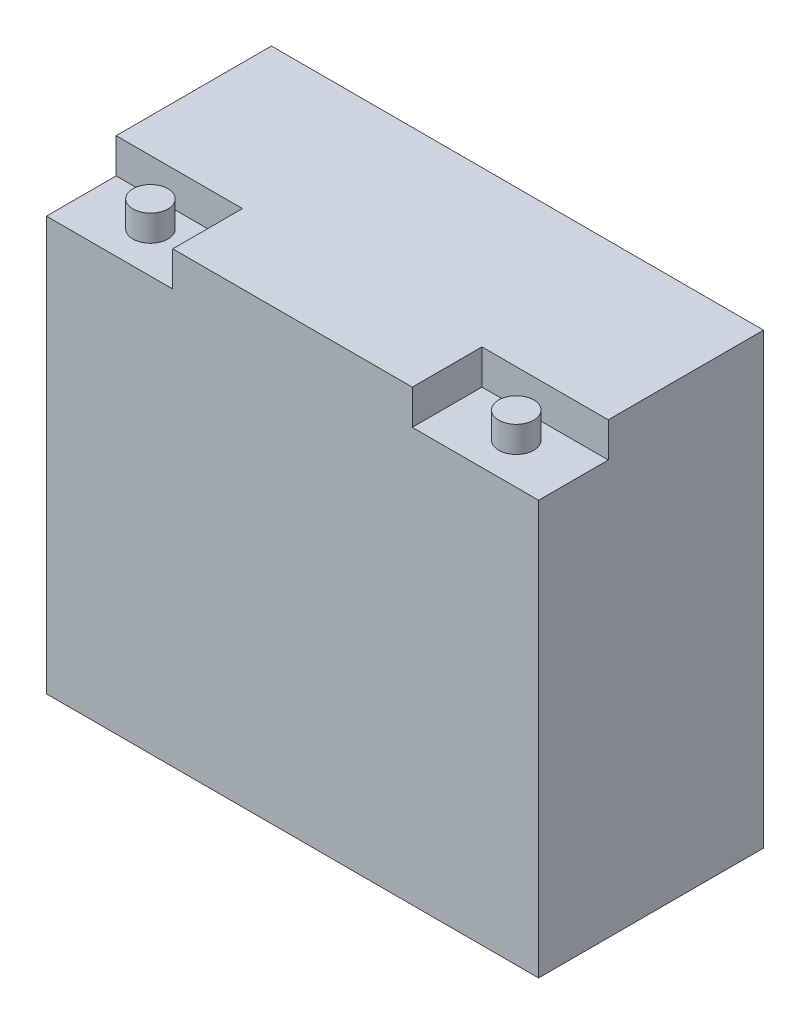
SolidWorks part; units mm, degrees
ref_plane "Front" through (0, 0, 0) normal (0, 0, 1) x (1, 0, 0)
ref_plane "Top" through (0, 0, 0) normal (0, 1, 0) x (1, 0, 0)
ref_plane "Right" through (0, 0, 0) normal (1, 0, 0) x (0, 0, -1)
sketch "Sketch1" plane through (0, 0, 0) normal (0, 1, 0) x (1, 0, 0)
  line L1 (0, 0) -> (179.3875, 0)
  line L2 (0, 0) -> (0, 82.0057)
  line L3 (0, 82.0057) -> (179.3875, 82.0057)
  line L4 (179.3875, 0) -> (179.3875, 82.0057)
  line L5 (0, 0) -> (179.3875, 82.0057) construction
  line L6 (0, 82.0057) -> (179.3875, 0) construction
  point P4 (89.6938, 41.0029)
  dimension "D1" = 179.3875
  dimension "D2" = 82.0057
extrude "Boss-Extrude1" add sketch "Sketch1" along normal blind 163.5125
sketch "Sketch2" plane through (0, 163.5125, 0) normal (0, 1, 0) x (1, 0, 0)
  line L0 (89.6938, 0) -> (89.6938, 82.0057) construction
  line L1 (0, 0) -> (46.0375, 0)
  line L2 (0, 0) -> (0, 25.4)
  line L3 (0, 25.4) -> (46.0375, 25.4)
  line L4 (46.0375, 0) -> (46.0375, 25.4)
  line L5 (0, 0) -> (46.0375, 25.4) construction
  line L6 (0, 25.4) -> (46.0375, 0) construction
  line L7 (0, 0) -> (179.3875, 0) construction
  line L8 (179.3875, 82.0057) -> (0, 82.0057) construction
  line L9 (179.3875, 25.4) -> (133.35, 0) construction
  line L10 (179.3875, 0) -> (133.35, 25.4) construction
  line L11 (133.35, 0) -> (133.35, 25.4)
  line L12 (179.3875, 25.4) -> (133.35, 25.4)
  line L13 (179.3875, 0) -> (179.3875, 25.4)
  line L14 (179.3875, 0) -> (133.35, 0)
  point P4 (23.0187, 12.7)
  point P16 (156.3688, 12.7)
extrude "Cut-Extrude1" cut sketch "Sketch2" against normal blind 12.7
sketch "Sketch3" plane through (0, 150.8125, 0) normal (0, 1, 0) x (1, 0, 0)
  line L1 (89.6938, 0) -> (89.6938, 82.0057) construction
  line L9 (46.0375, 0) -> (133.35, 0)
  line L10 (133.35, 0) -> (133.35, 25.4)
  line L11 (133.35, 25.4) -> (179.3875, 25.4)
  line L12 (179.3875, 25.4) -> (179.3875, 82.0057)
  line L13 (179.3875, 82.0057) -> (0, 82.0057)
  line L14 (0, 82.0057) -> (0, 25.4)
  line L15 (0, 25.4) -> (46.0375, 25.4)
  line L16 (46.0375, 25.4) -> (46.0375, 0)
  line L17 (46.0375, 0) -> (133.35, 0) construction
  line L18 (133.35, 0) -> (133.35, 25.4) construction
  line L19 (133.35, 25.4) -> (179.3875, 25.4) construction
  line L20 (179.3875, 25.4) -> (179.3875, 82.0057) construction
  line L21 (179.3875, 82.0057) -> (0, 82.0057) construction
  line L22 (0, 82.0057) -> (0, 25.4) construction
  line L23 (0, 25.4) -> (46.0375, 25.4) construction
  line L24 (46.0375, 25.4) -> (46.0375, 0) construction
  circle A0 centre (23.0187, 14.8862) radius 6.381
  circle A1 centre (156.3688, 14.8862) radius 6.381
  dimension "D1" = 0
extrude "Boss-Extrude2" add sketch "Sketch3" along normal blind 9.525
